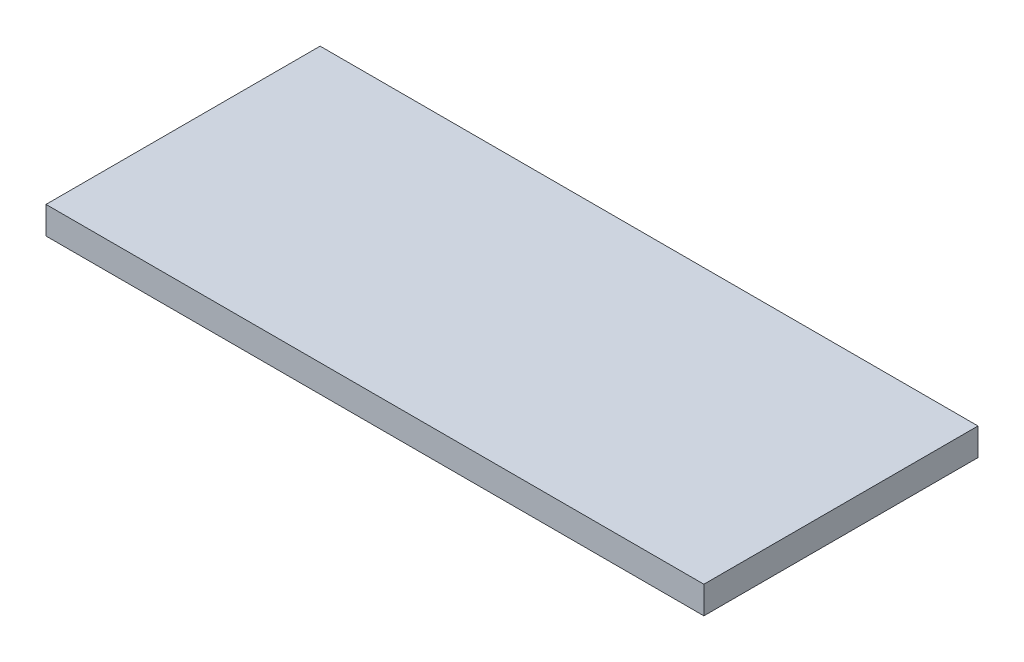
SolidWorks part; units mm, degrees
ref_plane "Front Plane" through (0, 0, 0) normal (0, 0, 1) x (1, 0, 0)
ref_plane "Top Plane" through (0, 0, 0) normal (0, 1, 0) x (1, 0, 0)
ref_plane "Right Plane" through (0, 0, 0) normal (1, 0, 0) x (0, 0, -1)
sketch "Sketch1" plane through (0, 0, 0) normal (0, 1, 0) x (1, 0, 0)
  line L1 (-66.2085, 10.782) -> (53.7915, 10.782)
  line L2 (-66.2085, 10.782) -> (-66.2085, -39.218)
  line L3 (-66.2085, -39.218) -> (53.7915, -39.218)
  line L4 (53.7915, 10.782) -> (53.7915, -39.218)
  line L5 (-66.2085, 10.782) -> (53.7915, -39.218) construction
  line L6 (-66.2085, -39.218) -> (53.7915, 10.782) construction
  point P4 (-6.2085, -14.218)
  dimension "D1" = 120
  dimension "D2" = 50
extrude "Boss-Extrude1" add sketch "Sketch1" along normal blind 5
